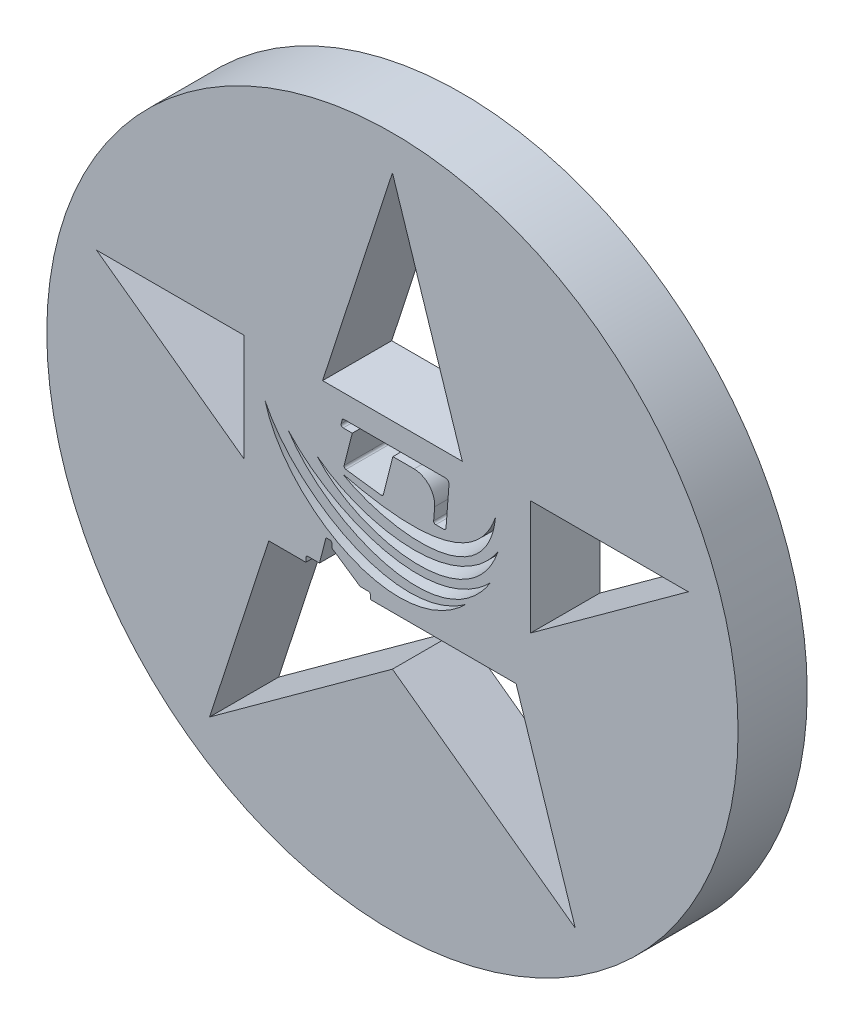
SolidWorks part; units mm, degrees
ref_plane "Front" through (0, 0, 0) normal (0, 0, 1) x (1, 0, 0)
ref_plane "Top" through (0, 0, 0) normal (0, 1, 0) x (1, 0, 0)
ref_plane "Right" through (0, 0, 0) normal (1, 0, 0) x (0, 0, -1)
sketch "草图1" plane through (0, 0, 0) normal (0, 0, 1) x (1, 0, 0)
  line L0 (0, 4.5) -> (-1.0103, 1.3906)
  line L1 (1.7204, -1.0058) -> (1.7889, -1.0058)
  line L3 (1.0103, 1.3906) -> (-1.0103, 1.3906)
  line L5 (0, -1.7188) -> (2.645, -3.6406)
  line L6 (2, -0.2658) -> (4.2798, 1.3906)
  line L7 (-2.15, 1.3906) -> (-2.15, -0.0666)
  line L8 (2, 1.3906) -> (2, -0.0227)
  line L9 (-1.7889, -1.0058) -> (1.7204, -1.0058)
  line L10 (-2.15, 1.3906) -> (-4.2798, 1.3906)
  line L11 (-0.7415, 0.9846) -> (-0.728, 1.0375)
  line L13 (-1.7889, -1.0058) -> (-2.645, -3.6406)
  line L14 (-0.699, 1.0601) -> (0.7684, 1.0601)
  line L17 (35.5655, 121.6074) -> (206.2322, 121.6074) construction
  line L18 (0.7449, 0.4046) -> (0.6263, 0.4046)
  line L19 (1.0103, 1.3906) -> (0, 4.5)
  line L20 (0.7748, 0.4324) -> (0.8183, 1.0064)
  line L22 (-0.7124, 0.9472) -> (-0.5809, 0.9472)
  line L23 (-0.5809, 0.9472) -> (-0.6987, 0.4834)
  line L24 (-0.6736, 0.4462) -> (-0.1648, 0.3793)
  line L25 (-0.1318, 0.4016) -> (0.0068, 0.9472)
  line L26 (0.5964, 0.4369) -> (0.6102, 0.6199)
  line L27 (0.0068, 0.9472) -> (0.3138, 0.9472)
  line L28 (-1.2528, -1.0058) -> (-1.2528, -0.9471)
  line L29 (-1.2228, -0.9171) -> (-1.0546, -0.9171)
  line L30 (-0.9619, -0.5523) -> (-1.0546, -0.9171)
  line L31 (-0.9619, -0.5523) -> (-0.9043, -0.5523)
  line L32 (-0.8743, -0.5823) -> (-0.8743, -0.6412)
  line L33 (-0.3184, -0.9471) -> (-0.3184, -1.0058)
  line L34 (-0.3484, -0.9171) -> (-0.4669, -0.9171)
  line L35 (-0.4669, -0.9171) -> (-0.8743, -0.6412)
  line L39 (-2.645, -3.6406) -> (0, -1.7188)
  line L40 (4.2798, 1.3906) -> (2, 1.3906)
  line L42 (-4.2798, 1.3906) -> (-2.15, -0.1568)
  line L43 (2.645, -3.6406) -> (1.7889, -1.0058)
  line L44 (-2.15, 1.3906) -> (-2.15, -0.1568)
  line L45 (2, 1.3906) -> (2, -0.2658)
  circle A0 centre (0, 0) radius 5
  arc A1 (0.6102, 0.6199) -> (0.3138, 0.9472) centre (0.3067, 0.6429) ccw
  arc A2 (0.8183, 1.0064) -> (0.7684, 1.0601) centre (0.7684, 1.0101) ccw
  arc A3 (-0.9043, -0.5523) -> (-0.8743, -0.5823) centre (-0.9043, -0.5823) cw
  arc A4 (-1.2528, -0.9471) -> (-1.2228, -0.9171) centre (-1.2228, -0.9471) cw
  arc A5 (-0.3484, -0.9171) -> (-0.3184, -0.9471) centre (-0.3484, -0.9471) cw
  arc A6 (-0.728, 1.0375) -> (-0.699, 1.0601) centre (-0.699, 1.0301) cw
  arc A7 (-0.7415, 0.9846) -> (-0.7124, 0.9472) centre (-0.7124, 0.9772) ccw
  arc A8 (-0.6987, 0.4834) -> (-0.6736, 0.4462) centre (-0.6697, 0.476) ccw
  arc A9 (-0.1648, 0.3793) -> (-0.1318, 0.4016) centre (-0.1609, 0.409) ccw
  arc A10 (0.6263, 0.4046) -> (0.5964, 0.4369) centre (0.6263, 0.4346) cw
  arc A11 (0.7748, 0.4324) -> (0.7449, 0.4046) centre (0.7449, 0.4346) cw
  spline S0 degree 3 poles (-0.7256, 0.3693) (-0.039, 0.1976) (1.1707, -0.0019) (1.4899, 0.9243) knots 0 0 0 0 1 1 1 1
  spline S1 degree 3 poles (-0.7256, 0.3693) (-0.0357, -0.0283) (1.3783, -0.1886) (1.4899, 0.9243) knots 0 0 0 0 1 1 1 1
  spline S2 degree 3 poles (-1.0898, 0.4046) (-0.3823, -0.1428) (0.9507, -0.3455) (1.5264, 0.5148) knots 0 0 0 0 1 1 1 1
  spline S3 degree 3 poles (-1.0898, 0.4046) (-0.4653, -0.3146) (1.1559, -0.5881) (1.5264, 0.5148) knots 0 0 0 0 1 1 1 1
  spline S4 degree 3 poles (-1.5029, 0.5148) (-0.8397, -0.2162) (0.601, -0.7546) (1.4168, 0.0716) knots 0 0 0 0 1 1 1 1
  spline S5 degree 3 poles (-1.5029, 0.5148) (-0.9357, -0.3591) (0.7257, -1.0404) (1.4168, 0.0716) knots 0 0 0 0 1 1 1 1
  spline S6 degree 3 poles (-1.8421, 0.7227) (-1.3936, -0.2079) (0.0987, -1.0881) (1.0672, -0.3727) knots 0 0 0 0 1 1 1 1
  spline S7 degree 3 poles (-1.8421, 0.7227) (-1.5341, -0.3984) (0.0995, -1.3283) (1.0672, -0.3727) knots 0 0 0 0 1 1 1 1
  dimension "D1" = 10
  dimension "D5" = 0.05
  dimension "D6" = 0.03
extrude "凸台-拉伸1" add sketch "草图1" along normal blind 1 contours A0 S7 S6 S5 S4 S3 S2 S1 S0 L7 L44 L42 L10 L19 L3 L0 L45 L8 L40 L6 L34 A5 L33 L9 L1 L43 L5 L39 L13 L28 A4 L29 L30 L31 A3 L32 L35 L20 A11 L18 A10
